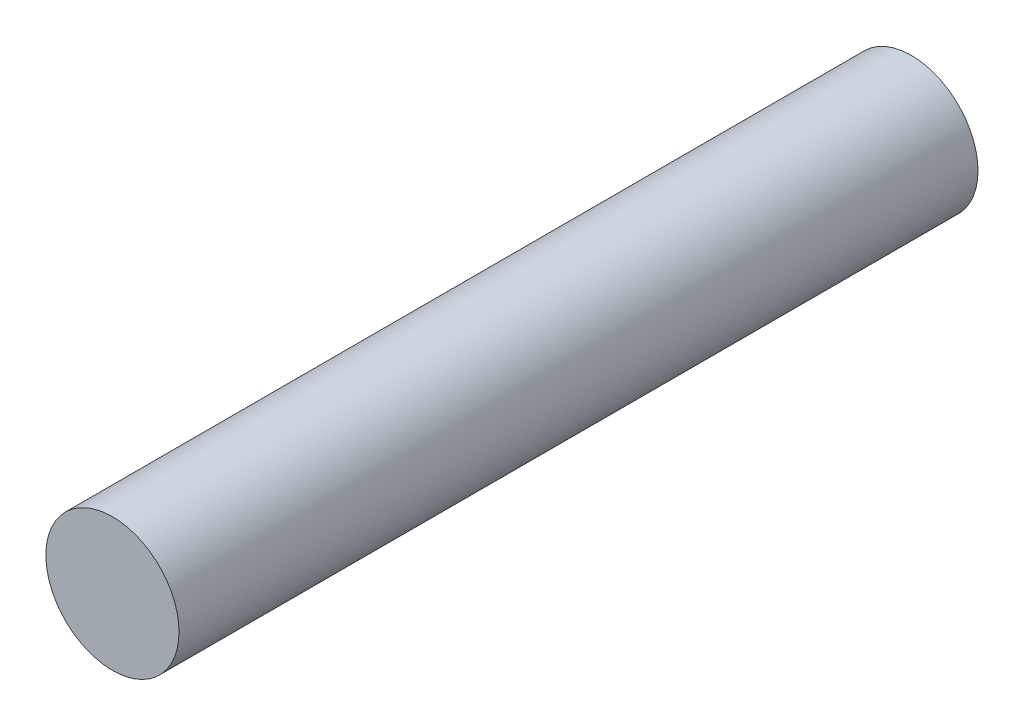
SolidWorks part; units mm, degrees
ref_plane "Front" through (0, 0, 0) normal (0, 0, 1) x (1, 0, 0)
ref_plane "Top" through (0, 0, 0) normal (0, 1, 0) x (1, 0, 0)
ref_plane "Right" through (0, 0, 0) normal (1, 0, 0) x (0, 0, -1)
sketch "Sketch1" plane through (0, 0, 0) normal (0, 0, 1) x (1, 0, 0)
  circle A0 centre (0, 0) radius 6.35
  dimension "D1" = 12.7
extrude "Boss-Extrude1" add sketch "Sketch1" along normal blind 76.2
